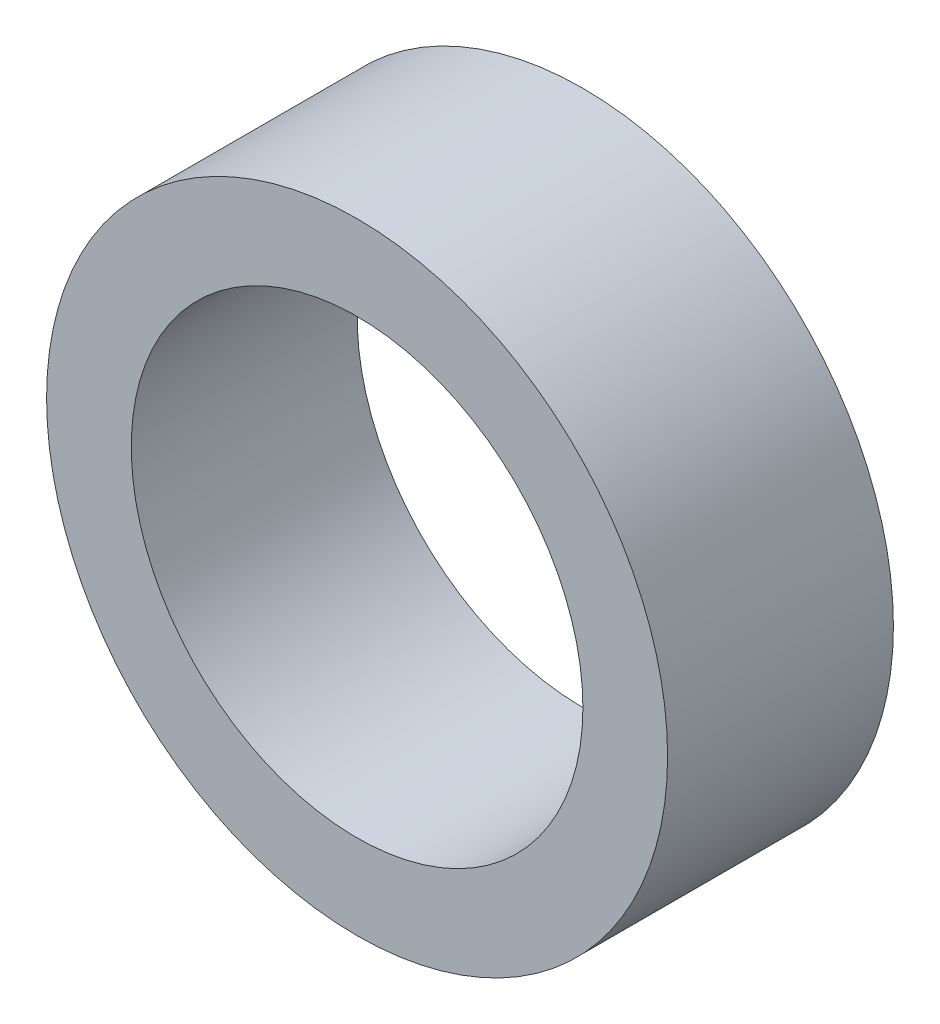
SolidWorks part; units mm, degrees
ref_plane "Alzado" through (0, 0, 0) normal (0, 0, 1) x (1, 0, 0)
ref_plane "Planta" through (0, 0, 0) normal (0, 1, 0) x (1, 0, 0)
ref_plane "Vista lateral" through (0, 0, 0) normal (1, 0, 0) x (0, 0, -1)
sketch "Croquis1" plane through (0, 0, 0) normal (0, 0, 1) x (1, 0, 0)
  circle A0 centre (0, 0) radius 8
  circle A1 centre (0, 0) radius 11
  dimension "D1" = 16
  dimension "D2" = 22
extrude "Saliente-Extruir1" add sketch "Croquis1" along normal blind 8
